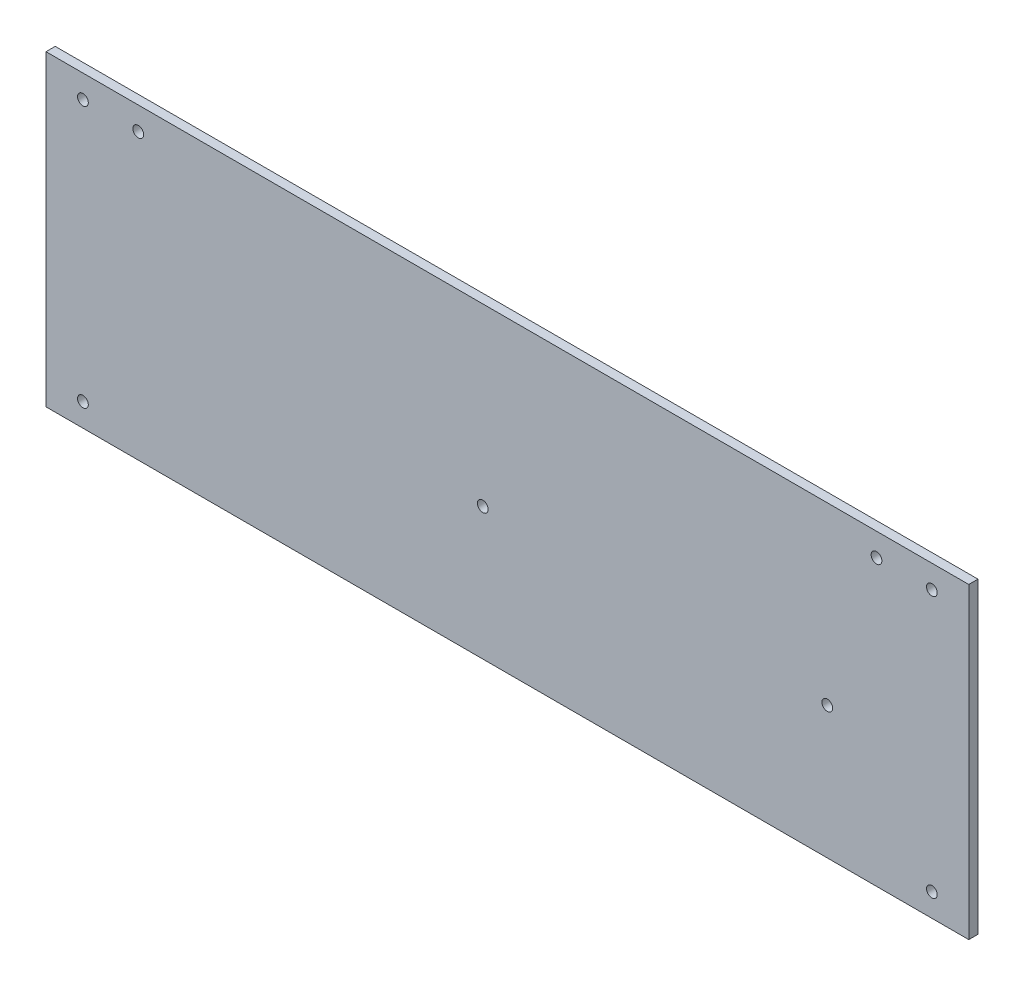
SolidWorks part; units mm, degrees
ref_plane "Front Plane" through (0, 0, 0) normal (0, 0, 1) x (1, 0, 0)
ref_plane "Top Plane" through (0, 0, 0) normal (0, 1, 0) x (1, 0, 0)
ref_plane "Right Plane" through (0, 0, 0) normal (1, 0, 0) x (0, 0, -1)
sketch "Sketch1" plane through (0, 0, 0) normal (0, 0, 1) x (1, 0, 0)
  line L1 (0, 0) -> (300, 0)
  line L2 (0, 0) -> (0, 100)
  line L3 (0, 100) -> (300, 100)
  line L4 (300, 0) -> (300, 100)
  dimension "D1" = 300
  dimension "D2" = 100
extrude "Boss-Extrude1" add sketch "Sketch1" along normal blind 3
sketch "Sketch6" plane through (0, 0, 3) normal (0, 0, 1) x (1, 0, 0)
  line L0 (300, 100) -> (0, 100) construction
  line L1 (300, 0) -> (300, 100) construction
  line L2 (198, 100) -> (198, 73.1678) construction
  circle A0 centre (142, 43) radius 1.75
  circle A1 centre (254, 43) radius 1.75
  dimension "D1" = 3.5
  dimension "D3" = 158
  dimension "D2" = 57
  dimension "D4" = 112
extrude "Cut-Extrude5" cut sketch "Sketch6" against normal blind 30
sketch "Sketch7" plane through (0, 0, 0) normal (0, 0, -1) x (-1, 0, 0)
  line L0 (-300, 0) -> (-300, 100) construction
  line L1 (-300, 100) -> (0, 100) construction
  line L2 (-150, 100) -> (-150, 79.5046) construction
  line L3 (-300, 50) -> (-270, 50) construction
  circle A0 centre (-288, 92.5) radius 1.75
  circle A1 centre (-270, 92.5) radius 1.75
  circle A2 centre (-288, 7.5) radius 1.75
  circle A3 centre (-12, 7.5) radius 1.75
  circle A4 centre (-12, 92.5) radius 1.75
  circle A5 centre (-30, 92.5) radius 1.75
  dimension "D1" = 3.5
  dimension "D2" = 12
  dimension "D3" = 7.5
  dimension "D4" = 30
extrude "Cut-Extrude6" cut sketch "Sketch7" against normal blind 10
